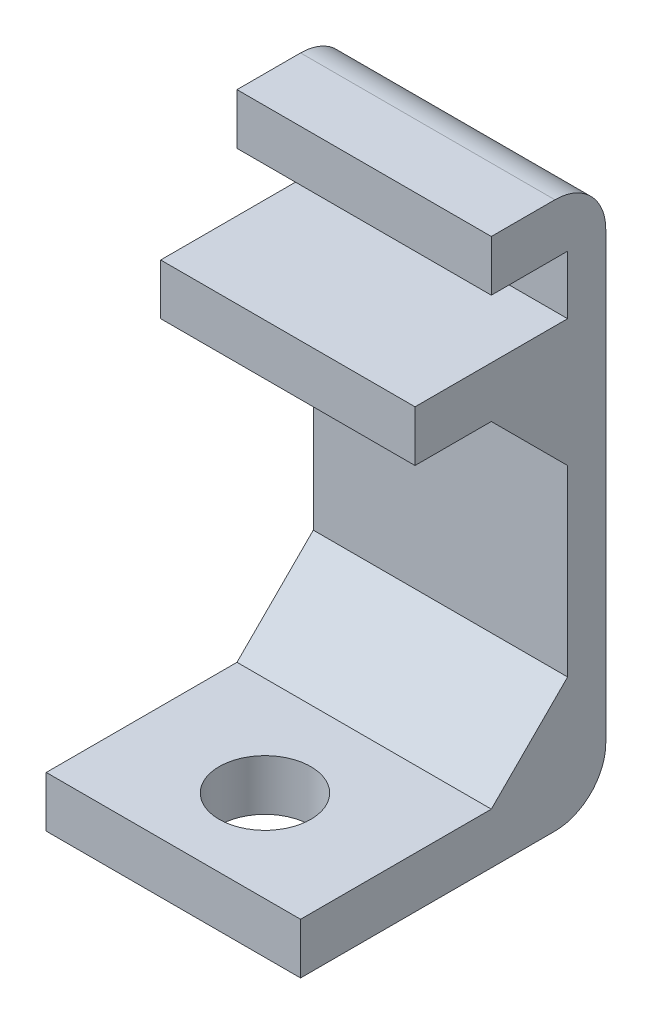
SolidWorks part; units mm, degrees
ref_plane "Plano frontal" through (0, 0, 0) normal (0, 0, 1) x (1, 0, 0)
ref_plane "Plano superior" through (0, 0, 0) normal (0, 1, 0) x (1, 0, 0)
ref_plane "Plano direito" through (0, 0, 0) normal (1, 0, 0) x (0, 0, -1)
sketch "Sketch1" plane through (0, 0, 0) normal (1, 0, 0) x (0, 0, -1)
  line L0 (-5.25, -8.75) -> (-5.25, -10.75)
  line L1 (2.25, 10.75) -> (6.75, 10.75)
  line L2 (2.25, 10.75) -> (2.25, 8.75)
  line L3 (-5.25, -10.75) -> (6.75, -10.75)
  line L4 (6.75, 10.75) -> (6.75, -10.75)
  line L5 (2.25, 8.75) -> (5.25, 8.75)
  line L7 (-5.25, -8.75) -> (5.25, -8.75)
  line L8 (5.25, 8.75) -> (5.25, 6.45)
  line L9 (5.25, 4.45) -> (5.25, -8.75)
  line L10 (-0.75, 6.45) -> (5.25, 6.45)
  line L11 (-0.75, 6.45) -> (-0.75, 4.45)
  line L12 (-0.75, 4.45) -> (5.25, 4.45)
  point P7 (6.75, 0)
  point P15 (0, -8.75)
  dimension "D1" = 17.2
  dimension "D2" = 4.5
  dimension "D3" = 1.5
  dimension "D4" = 2
  dimension "D5" = 2.3
  dimension "D6" = 12
  dimension "D7" = 6
extrude "Boss-Extrude1" add sketch "Sketch1" along normal mid plane 10 contours L5 L8 L7 L2 L3 L4 L1
chamfer "Chamfer1" distance 3 angle 45 2 edges at (0, 4.45, -5.25) (0, -8.75, -5.25)
sketch "Sketch2" plane through (0, -8.75, 0) normal (0, 1, 0) x (1, 0, 0)
  line L2 (5, -5.25) -> (-5, -5.25) construction
  circle A0 centre (0, -1.65) radius 1.5 construction
  circle A1 centre (0, -1.65) radius 1.8
  dimension "D1" = 3
  dimension "D3" = 1.8
  dimension "D2" = 0.3
extrude "Cut-Extrude1" cut sketch "Sketch2" against normal through all and the other way blind 3
fillet "Fillet1" radius 2 2 edges at (0, -10.75, -6.75) (0, 10.75, -6.75)
